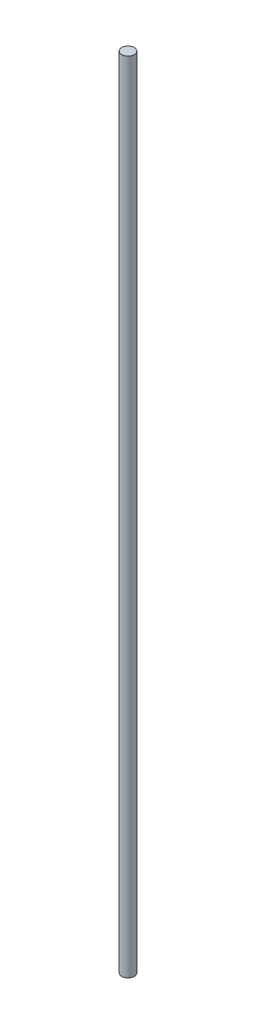
SolidWorks part; units mm, degrees
ref_plane "Front Plane" through (0, 0, 0) normal (0, 0, 1) x (1, 0, 0)
ref_plane "Top Plane" through (0, 0, 0) normal (0, 1, 0) x (1, 0, 0)
ref_plane "Right Plane" through (0, 0, 0) normal (1, 0, 0) x (0, 0, -1)
sketch "Sketch1" plane through (0, 0, 0) normal (0, 1, 0) x (1, 0, 0)
  circle A0 centre (0, 0) radius 1.5875
  dimension "D1" = 3.175
extrude "Boss-Extrude1" add sketch "Sketch1" along normal blind 203.2
